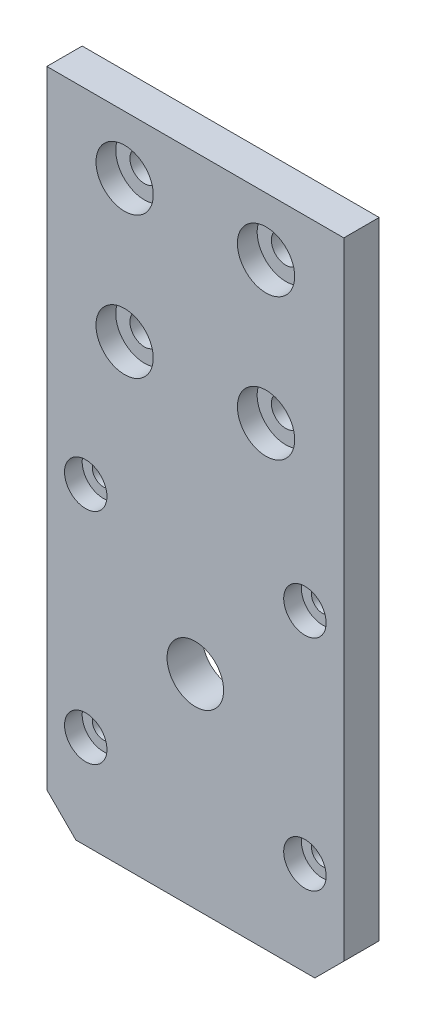
SolidWorks part; units mm, degrees
ref_plane "Alzado" through (0, 0, 0) normal (0, 0, 1) x (1, 0, 0)
ref_plane "Planta" through (0, 0, 0) normal (0, 1, 0) x (1, 0, 0)
ref_plane "Vista lateral" through (0, 0, 0) normal (1, 0, 0) x (0, 0, -1)
sketch "Croquis1" plane through (0, 0, 0) normal (0, 0, 1) x (1, 0, 0)
  line L0 (11, 56.8) -> (31, 76.8) construction
  line L1 (0, 85) -> (42, 85)
  line L2 (0, 85) -> (0, 0)
  line L3 (0, 0) -> (42, 0)
  line L4 (42, 85) -> (42, 0)
  line L5 (21, 66.8) -> (21, 85) construction
  circle A0 centre (11, 76.8) radius 2.05
  circle A1 centre (31, 76.8) radius 2.05
  circle A4 centre (31, 56.8) radius 2.05
  circle A5 centre (11, 56.8) radius 2.05
  dimension "D3" = 4.1
  dimension "D1" = 42
  dimension "D2" = 85
  dimension "D4" = 20
  dimension "D6" = 8.2
  dimension "D7" = 20
extrude "Saliente-Extruir1" add sketch "Croquis1" along normal blind 5
sketch "Croquis4" plane through (0, 0, 5) normal (0, 0, 1) x (1, 0, 0)
  circle A0 centre (11, 76.8) radius 4.05
  circle A1 centre (11, 56.8) radius 4.05
  circle A2 centre (31, 56.8) radius 4.05
  circle A3 centre (31, 76.8) radius 4.05
  dimension "D1" = 8.1
extrude "Cortar-Extruir1" cut sketch "Croquis4" against normal blind 2.8
sketch "Croquis5" plane through (0, 0, 5) normal (0, 0, 1) x (1, 0, 0)
  line L0 (5.5, 36.58) -> (36.5, 5.58) construction
  line L1 (0, 85) -> (42, 85) construction
  line L2 (36.5, 36.58) -> (5.5, 5.58) construction
  line L3 (21, 21.08) -> (21, 0) construction
  line L4 (0, 0) -> (42, 0) construction
  circle A0 centre (21, 21.08) radius 11.5 construction
  circle A1 centre (5.5, 36.58) radius 1.575
  circle A2 centre (36.5, 36.58) radius 1.575
  circle A3 centre (36.5, 5.58) radius 1.575
  circle A4 centre (5.5, 5.58) radius 1.575
  circle A5 centre (21, 21.08) radius 4
  dimension "D1" = 23
  dimension "D4" = 3.15
  dimension "D2" = 31
  dimension "D3" = 31
  dimension "D5" = 63.92
extrude "Cortar-Extruir2" cut sketch "Croquis5" against normal through all
sketch "Croquis6" plane through (0, 0, 5) normal (0, 0, 1) x (1, 0, 0)
  circle A0 centre (5.5, 36.58) radius 3
  circle A1 centre (36.5, 36.58) radius 3
  circle A2 centre (36.5, 5.58) radius 3
  circle A4 centre (5.5, 5.58) radius 3
  dimension "D1" = 6
extrude "Cortar-Extruir3" cut sketch "Croquis6" against normal blind 2.5
sketch "Croquis7" plane through (0, 0, 0) normal (0, 0, -1) x (-1, 0, 0)
  line L1 (-42, 0) -> (0, 0)
  line L2 (-42, 0) -> (-42, -7.7)
  line L3 (-42, -7.7) -> (0, -7.7)
  line L4 (0, 0) -> (0, -7.7)
  dimension "D1" = 7.7
extrude "Saliente-Extruir2" add sketch "Croquis7" against normal through all
chamfer "Chaflán1" distance 4.1 angle 45 2 edges at (0, -7.7, 2.5) (42, -7.7, 2.5)
